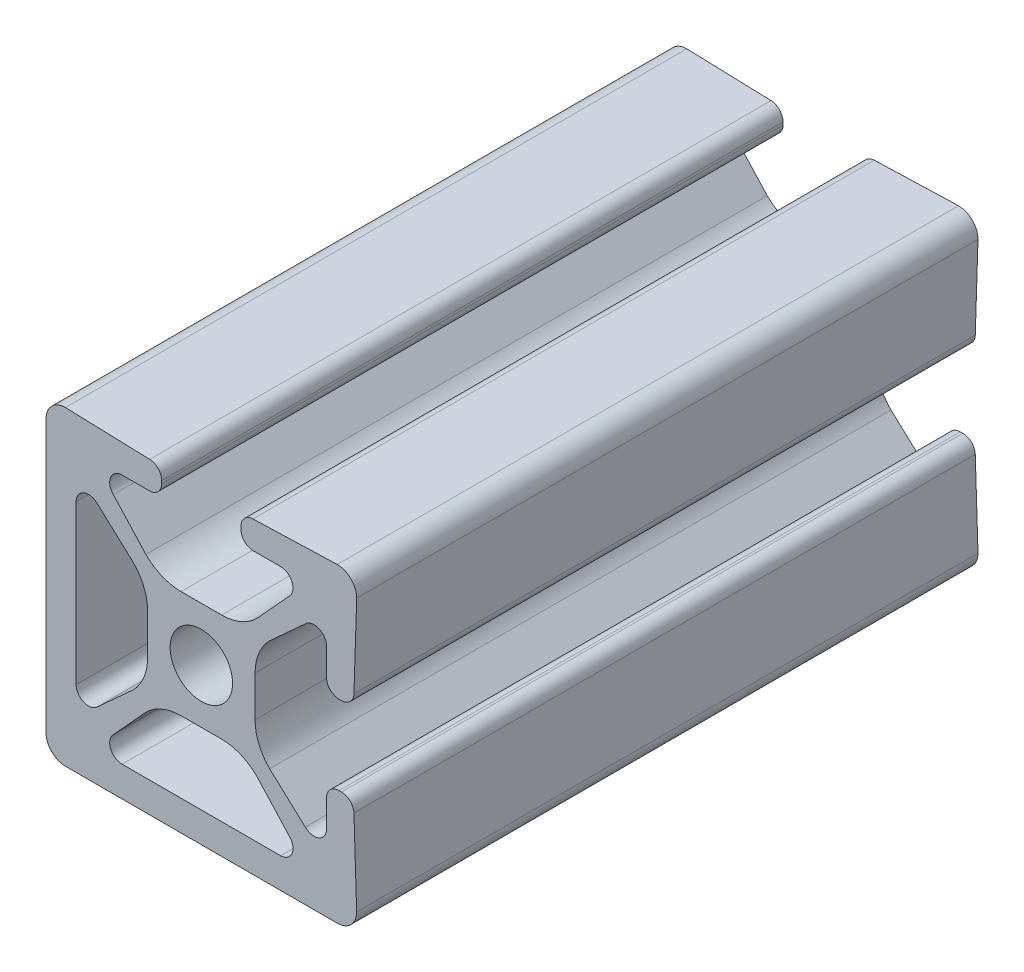
SolidWorks part; units mm, degrees
material "6061 Alloy"
ref_plane "Front" through (0, 0, 0) normal (0, 0, 1) x (1, 0, 0)
ref_plane "Top" through (0, 0, 0) normal (0, 1, 0) x (1, 0, 0)
ref_plane "Right" through (0, 0, 0) normal (1, 0, 0) x (0, 0, -1)
sketch "Sketch1" plane through (0, 0, 0) normal (0, 0, 1) x (1, 0, 0)
  line L0 (-5.1181, -3.2385) -> (-5.1181, 3.2392)
  line L1 (-2.7923, -2.2661) -> (-4.2509, -3.597)
  line L2 (-4.2509, 3.5977) -> (-2.7922, 2.2661)
  line L3 (-2.1971, 0.8292) -> (-2.1971, -0.8292)
  line L4 (-2.2661, 2.7923) -> (-3.5977, 4.2509)
  line L5 (-0.8292, 2.1971) -> (0.8292, 2.1971)
  line L6 (-3.2392, 5.1181) -> (-2.1273, 5.1181)
  line L7 (2.2661, 2.7923) -> (3.597, 4.2509)
  line L8 (-1.6193, 5.6261) -> (-1.6193, 5.7311)
  line L9 (3.2385, 5.1181) -> (2.1273, 5.1181)
  line L10 (-2.1109, 6.2389) -> (-5.5562, 6.35)
  line L11 (1.6193, 5.6261) -> (1.6193, 5.7311)
  line L12 (-6.35, 5.5562) -> (-6.35, -5.5562)
  line L13 (5.5562, 6.35) -> (2.1109, 6.2389)
  line L14 (-5.5562, -6.35) -> (5.5562, -6.35)
  line L15 (6.2389, 2.1109) -> (6.35, 5.5562)
  line L16 (6.35, -5.5562) -> (6.2388, -2.1109)
  line L17 (5.6261, 1.6193) -> (5.7311, 1.6193)
  line L18 (5.7311, -1.6193) -> (5.6261, -1.6193)
  line L19 (5.1181, 3.2385) -> (5.1181, 2.1273)
  line L20 (5.1181, -2.1273) -> (5.1181, -3.2392)
  line L21 (2.7923, 2.2661) -> (4.2509, 3.597)
  line L22 (4.2509, -3.5977) -> (2.7923, -2.2661)
  line L23 (2.1971, -0.8292) -> (2.1971, 0.8292)
  line L24 (0.8292, -2.1971) -> (-0.8292, -2.1971)
  line L25 (-2.2661, -2.7923) -> (-3.597, -4.2509)
  line L26 (3.5977, -4.2509) -> (2.2661, -2.7922)
  line L27 (-3.2385, -5.1181) -> (3.2392, -5.1181)
  arc A0 (-5.1181, -3.2385) -> (-4.2509, -3.597) centre (-4.6101, -3.2378) ccw
  arc A1 (-4.2509, 3.5977) -> (-5.1181, 3.2392) centre (-4.6101, 3.2385) ccw
  arc A2 (-2.7923, -2.2661) -> (-2.1971, -0.8292) centre (-4.2291, -0.8292) ccw
  arc A3 (-2.1971, 0.8292) -> (-2.7922, 2.2661) centre (-4.2291, 0.8292) ccw
  circle A4 centre (0, 0) radius 1.2764
  arc A5 (-2.2661, 2.7923) -> (-0.8292, 2.1971) centre (-0.8292, 4.2291) ccw
  arc A6 (-3.2392, 5.1181) -> (-3.5977, 4.2509) centre (-3.2385, 4.6101) ccw
  arc A7 (0.8292, 2.1971) -> (2.2661, 2.7923) centre (0.8292, 4.2292) ccw
  arc A8 (-2.1273, 5.1181) -> (-1.6193, 5.6261) centre (-2.1273, 5.6261) ccw
  arc A9 (3.597, 4.2509) -> (3.2385, 5.1181) centre (3.2378, 4.6101) ccw
  arc A10 (-1.6193, 5.7311) -> (-2.1109, 6.2389) centre (-2.1273, 5.7311) ccw
  arc A11 (1.6193, 5.6261) -> (2.1273, 5.1181) centre (2.1273, 5.6261) ccw
  arc A12 (-5.5562, 6.35) -> (-6.35, 5.5562) centre (-5.5562, 5.5562) ccw
  arc A13 (2.1109, 6.2389) -> (1.6193, 5.7311) centre (2.1273, 5.7311) ccw
  arc A14 (-6.35, -5.5562) -> (-5.5562, -6.35) centre (-5.5562, -5.5562) ccw
  arc A15 (6.35, 5.5562) -> (5.5562, 6.35) centre (5.5562, 5.5562) ccw
  arc A16 (5.5562, -6.35) -> (6.35, -5.5562) centre (5.5562, -5.5562) ccw
  arc A17 (5.7311, 1.6193) -> (6.2389, 2.1109) centre (5.7311, 2.1273) ccw
  arc A18 (6.2388, -2.1109) -> (5.7311, -1.6193) centre (5.7311, -2.1273) ccw
  arc A19 (5.1181, 2.1273) -> (5.6261, 1.6193) centre (5.6261, 2.1273) ccw
  arc A20 (5.6261, -1.6193) -> (5.1181, -2.1273) centre (5.6261, -2.1273) ccw
  arc A21 (5.1181, 3.2385) -> (4.2509, 3.597) centre (4.6101, 3.2378) ccw
  arc A22 (4.2509, -3.5977) -> (5.1181, -3.2392) centre (4.6101, -3.2385) ccw
  arc A23 (2.7923, 2.2661) -> (2.1971, 0.8292) centre (4.2292, 0.8292) ccw
  arc A24 (2.1971, -0.8292) -> (2.7923, -2.2661) centre (4.2291, -0.8292) ccw
  arc A25 (-0.8292, -2.1971) -> (-2.2661, -2.7923) centre (-0.8292, -4.2291) ccw
  arc A26 (2.2661, -2.7922) -> (0.8292, -2.1971) centre (0.8292, -4.2291) ccw
  arc A27 (-3.597, -4.2509) -> (-3.2385, -5.1181) centre (-3.2378, -4.6101) ccw
  arc A28 (3.2392, -5.1181) -> (3.5977, -4.2509) centre (3.2385, -4.6101) ccw
extrude "Extrude1" add sketch "Sketch1" along normal blind 25.4
